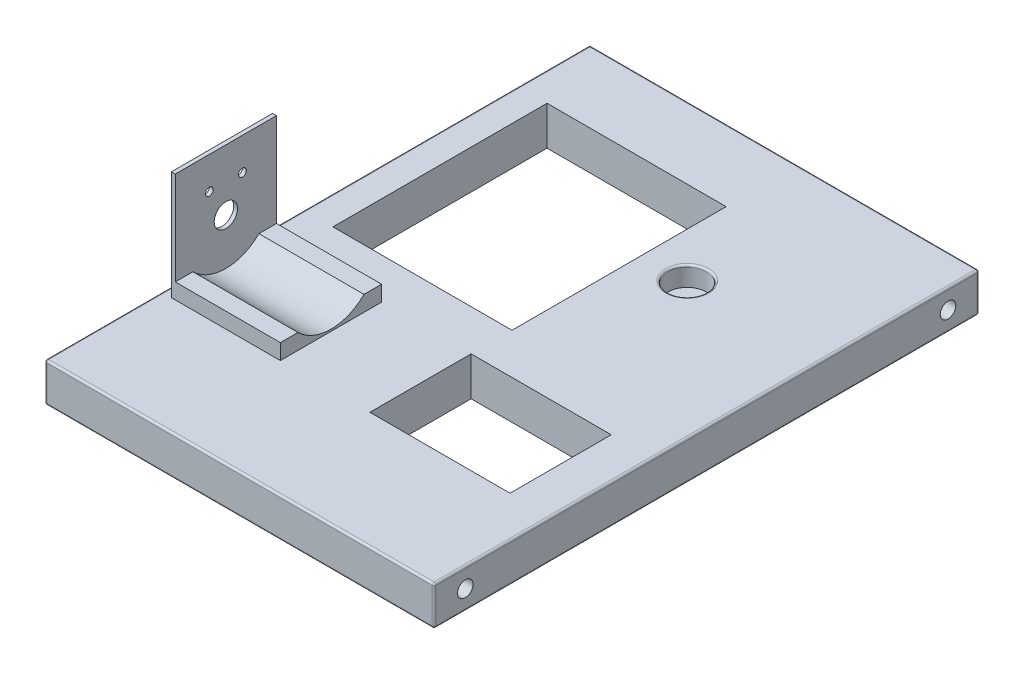
SolidWorks part; units mm, degrees
material "ABS"
ref_plane "Front Plane" through (0, 0, 0) normal (0, 0, 1) x (1, 0, 0)
ref_plane "Top Plane" through (0, 0, 0) normal (0, 1, 0) x (1, 0, 0)
ref_plane "Right Plane" through (0, 0, 0) normal (1, 0, 0) x (0, 0, -1)
sketch "Sketch2" plane through (0, 0, 0) normal (0, 1, 0) x (1, 0, 0)
  line L0 (0, 0) -> (0, 140)
  line L1 (0, 140) -> (100, 140)
  line L2 (100, 140) -> (100, 0)
  line L3 (100, 0) -> (0, 0)
  dimension "D1" = 100
  dimension "D2" = 140
extrude "Boss-Extrude1" add sketch "Sketch2" along normal blind 10
sketch "Sketch3" plane through (0, 10, 0) normal (0, 1, 0) x (1, 0, 0)
  line L0 (100, 0) -> (100, 140) construction
  circle A0 centre (65, 100) radius 5
  dimension "D2" = 10
  dimension "D1" = 35
extrude "MountHole" cut sketch "Sketch3" against normal blind 5
sketch "Sketch4" plane through (0, 0, 0) normal (-1, 0, 0) x (0, 0, 1)
  line L0 (-8, 10) -> (-8, 0) construction
  line L1 (-140, 10) -> (0, 10) construction
  line L2 (-140, 0) -> (0, 0) construction
  line L3 (0, 10) -> (0, 0) construction
  circle A0 centre (-8, 5) radius 2
  dimension "D2" = 4
  dimension "D1" = 8
extrude "Cut-Extrude2" cut sketch "Sketch4" against normal through all
sketch "Sketch5" plane through (0, 0, 0) normal (-1, 0, 0) x (0, 0, 1)
  line L0 (-132, 10) -> (-132, 0) construction
  line L1 (-140, 10) -> (0, 10) construction
  line L2 (-140, 0) -> (0, 0) construction
  line L3 (-140, 10) -> (-140, 0) construction
  circle A0 centre (-132, 5) radius 2
  dimension "D2" = 4
  dimension "D1" = 8
extrude "Cut-Extrude3" cut sketch "Sketch5" against normal through all
fillet "Fillet1" [suppressed] radius 2
fillet "Fillet4" radius 0.5 12 edges at (50, 0, -140) (100, 5, -140) (50, 10, -140) (0, 5, -140) (0, 0, -70) (0, 10, -70) (100, 0, -70) (100, 10, -70) (100, 5, 0) (50, 0, 0) (50, 10, 0) (0, 5, 0)
fillet "Fillet6" radius 0.5 1 edges at (65, 10, -95)
sketch "Sketch7" plane through (0, 10, 0) normal (0, 1, 0) x (1, 0, 0)
  line L0 (11, 0) -> (11, 43) construction
  line L1 (0, 0) -> (100, 0) construction
  line L2 (0, 140) -> (0, 0) construction
  line L3 (11, 43) -> (47.1706, 43) construction
  line L9 (11, 43) -> (-5.1328, 43) construction
  line L15 (2.5, 56) -> (2.5, 30)
  line L16 (2.5, 56) -> (30.5, 56)
  line L17 (30.5, 56) -> (30.5, 30)
  line L18 (30.5, 30) -> (2.5, 30)
  point P10 (2.5, 43)
  dimension "D1" = 43
  dimension "D2" = 11
  dimension "D3" = 26
  dimension "D4" = 28
  dimension "D5" = 8.5
extrude "Boss-Extrude2" add sketch "Sketch7" along normal blind 4
sketch "Sketch21" plane through (0, 10, 0) normal (0, 1, 0) x (1, 0, 0)
  line L0 (30.5, 56) -> (2.5, 56) construction
  line L5 (7.5, 121.5) -> (53.5, 121.5)
  line L6 (7.5, 121.5) -> (7.5, 66.5)
  line L7 (7.5, 66.5) -> (53.5, 66.5)
  line L8 (53.5, 121.5) -> (53.5, 66.5)
  line L9 (7.5, 121.5) -> (53.5, 66.5) construction
  line L10 (7.5, 66.5) -> (53.5, 121.5) construction
  line L12 (0.5, 139.5) -> (0.5, 0.5) construction
  line L13 (30.5, 56) -> (101.6561, 56) construction
  line L14 (30.5, 30) -> (101.6561, 30) construction
  line L15 (53.5, 56) -> (53.5, 30)
  line L20 (53.5, 30) -> (89.5, 30)
  line L21 (89.5, 30) -> (89.5, 56)
  line L22 (89.5, 56) -> (53.5, 56)
  point P0 (30.5, 94)
  dimension "D1" = 46
  dimension "D2" = 55
  dimension "D3" = 38
  dimension "D4" = 30
  dimension "D5" = 36
extrude "Cut-Extrude10" cut sketch "Sketch21" against normal through all
sketch "Sketch10" plane through (0, 14, 0) normal (0, 1, 0) x (1, 0, 0)
  line L0 (2.5, 56) -> (2.5, 30)
  line L1 (2.5, 30) -> (3.5, 30)
  line L2 (2.5, 30) -> (30.5, 30) construction
  line L3 (3.5, 30) -> (3.5, 56)
  line L4 (30.5, 56) -> (2.5, 56) construction
  line L5 (3.5, 56) -> (2.5, 56)
  dimension "D1" = 1
extrude "Boss-Extrude3" add sketch "Sketch10" along normal blind 24
sketch "Sketch13" plane through (2.5, 0, 0) normal (-1, 0, 0) x (0, 0, 1)
  line L0 (-43, 10) -> (-43, 22.354) construction
  line L1 (-56, 10) -> (-30, 10) construction
  line L2 (-43, 22.354) -> (-38.75, 29.7152) construction
  line L3 (-43, 22.354) -> (-6.4369, 22.354) construction
  line L4 (-43, 22.354) -> (-47.25, 29.7152) construction
  circle A0 centre (-43, 22.354) radius 3
  circle A1 centre (-38.75, 29.7152) radius 1
  circle A2 centre (-47.25, 29.7152) radius 1
  dimension "D2" = 6
  dimension "D5" = 2
  dimension "D8" = 2
  dimension "D1" = 12.354
  dimension "D3" = 60
  dimension "D4" = 8.5
  dimension "D6" = 120
  dimension "D7" = 8.5
extrude "Cut-Extrude6" cut sketch "Sketch13" against normal up to surface (1 mm away) up to face at (3.5, 26, -43)
sketch "Sketch20" plane through (30.5, 0, 0) normal (1, 0, 0) x (0, 0, -1)
  line L0 (43, 10) -> (43, 39.7821) construction
  line L2 (30, 10) -> (56, 10) construction
  line L3 (30, 14) -> (56, 14) construction
  line L4 (30, 14) -> (56, 14) construction
  line L5 (30, 14) -> (34.5198, 14)
  line L6 (51.4802, 14) -> (56, 14)
  arc A0 (34.5198, 14) -> (51.4802, 14) centre (43, 22.4904) ccw
  dimension "D1" = 12
extrude "Cut-Extrude9" cut sketch "Sketch20" against normal blind 27 and the other way through all
